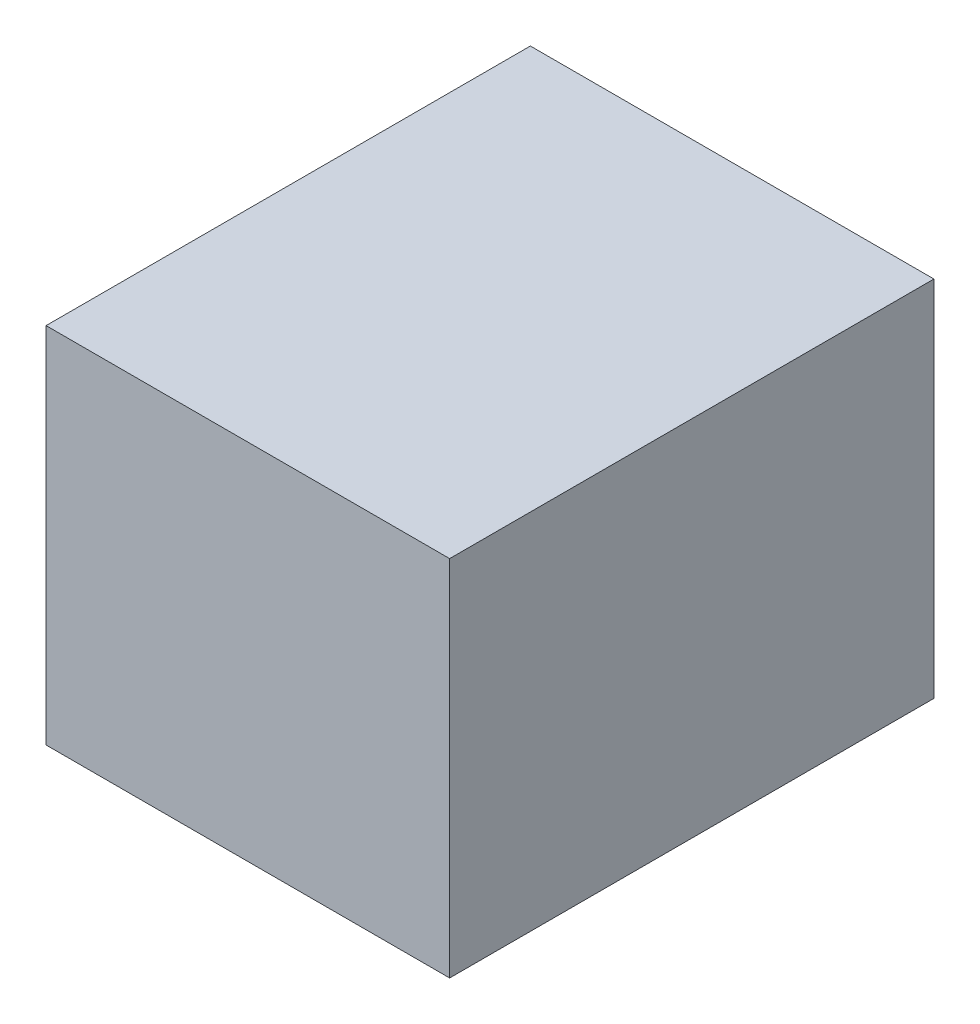
SolidWorks part; units mm, degrees
ref_plane "Front Plane" through (0, 0, 0) normal (0, 0, 1) x (1, 0, 0)
ref_plane "Top Plane" through (0, 0, 0) normal (0, 1, 0) x (1, 0, 0)
ref_plane "Right Plane" through (0, 0, 0) normal (1, 0, 0) x (0, 0, -1)
sketch "Sketch1" plane through (0, 0, 0) normal (0, 1, 0) x (1, 0, 0)
  line L1 (0, 0) -> (500, 0)
  line L2 (0, 0) -> (0, 600)
  line L3 (0, 600) -> (500, 600)
  line L4 (500, 0) -> (500, 600)
extrude "Boss-Extrude1" add sketch "Sketch1" along normal blind 450
sketch "Sketch2" plane through (0, 0, 0) normal (-1, 0, 0) x (0, 0, 1)
  line L0 (-575, 425) -> (-25, 425)
  line L1 (-600, 450) -> (0, 450)
  line L2 (-600, 450) -> (-600, 0)
  line L3 (-600, 0) -> (0, 0)
  line L4 (0, 450) -> (0, 0)
  line L5 (-25, 425) -> (-25, 225)
  line L6 (-575, 25) -> (-25, 25)
  line L7 (-575, 425) -> (-575, 225)
  line L8 (-575, 225) -> (-25, 225)
  line L9 (-575, 200) -> (-25, 200)
  line L10 (-575, 200) -> (-575, 25)
  line L11 (-575, 425) -> (-575, 25) construction
  line L12 (-25, 200) -> (-25, 25)
  line L13 (-25, 425) -> (-25, 25) construction
  dimension "D1" = 25
  dimension "D2" = 25
extrude "Cut-Extrude2" cut sketch "Sketch2" against normal offset from surface (475 mm away) 25 contours L0 L5 L8 L7 | L6 L12 L9 L10 up to face at (500, 225, -300)
